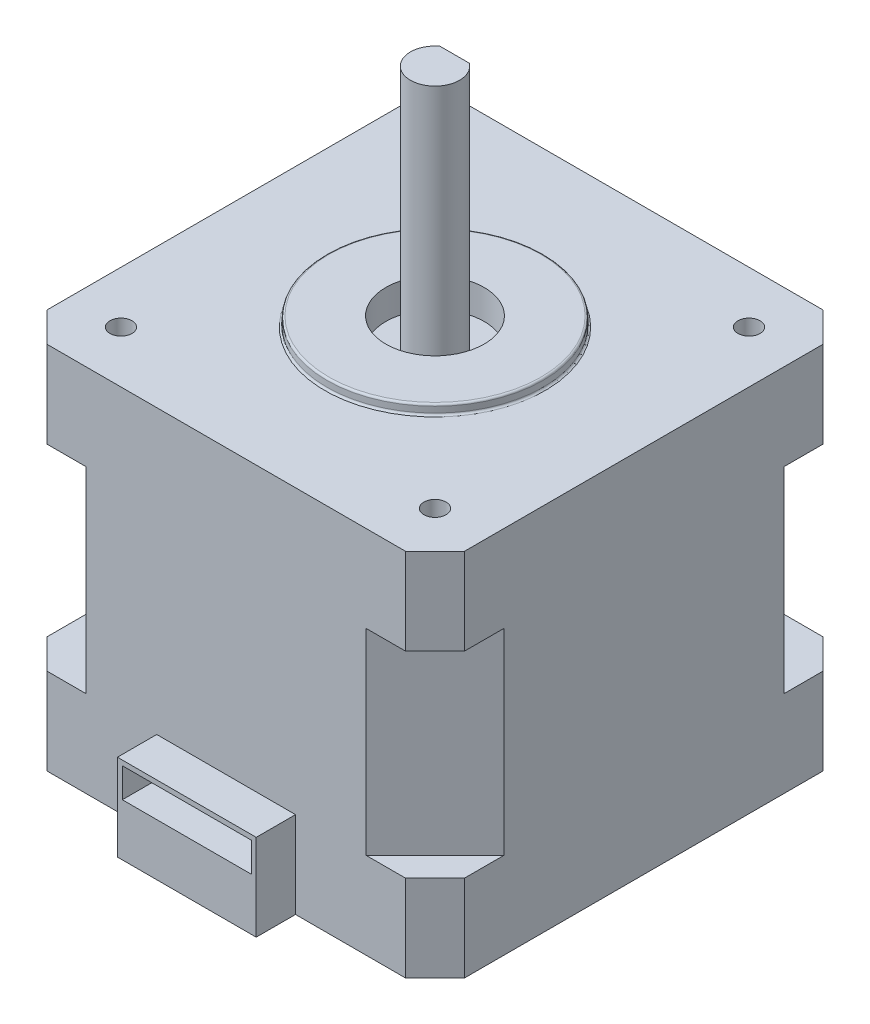
SolidWorks part; units mm, degrees
ref_plane "Front Plane" through (0, 0, 0) normal (0, 0, 1) x (1, 0, 0)
ref_plane "Top Plane" through (0, 0, 0) normal (0, 1, 0) x (1, 0, 0)
ref_plane "Right Plane" through (0, 0, 0) normal (1, 0, 0) x (0, 0, -1)
sketch "Sketch1" plane through (0, 0, 0) normal (0, 1, 0) x (1, 0, 0)
  line L0 (-21.25, 18.25) -> (-18.25, 21.25)
  line L1 (-18.25, -21.25) -> (18.25, -21.25)
  line L2 (-21.25, -18.25) -> (-21.25, 18.25)
  line L3 (-18.25, 21.25) -> (18.25, 21.25)
  line L4 (21.25, -18.25) -> (21.25, 18.25)
  line L5 (-21.25, -21.25) -> (21.25, 21.25) construction
  line L6 (-21.25, 21.25) -> (21.25, -21.25) construction
  line L7 (18.25, 21.25) -> (21.25, 18.25)
  line L8 (18.25, -21.25) -> (21.25, -18.25)
  line L9 (-21.25, -18.25) -> (-18.25, -21.25)
  point P0 (0, 0)
  dimension "D1" = 42.5
  dimension "D2" = 42.5
extrude "Boss-Extrude1" add sketch "Sketch1" along normal mid plane 37.6
sketch "Sketch2" plane through (0, 0, 0) normal (0, 1, 0) x (1, 0, 0)
  line L1 (-21.25, 18.25) -> (-21.25, -18.25) construction
  line L2 (18.25, 21.25) -> (-18.25, 21.25) construction
  line L5 (21.25, -18.25) -> (21.25, 18.25) construction
  line L16 (-21.25, 14.25) -> (-21.25, -14.25)
  line L17 (-21.25, -14.25) -> (-14.25, -21.25)
  line L18 (-14.25, -21.25) -> (14.25, -21.25)
  line L19 (14.25, -21.25) -> (21.25, -14.25)
  line L20 (21.25, -14.25) -> (21.25, 14.25)
  line L21 (21.25, 14.25) -> (14.25, 21.25)
  line L22 (14.25, 21.25) -> (-14.25, 21.25)
  line L23 (-14.25, 21.25) -> (-21.25, 14.25)
  dimension "D1" = 42.5
  dimension "D2" = 42.5
  dimension "D3" = 9.8995
  dimension "D4" = 7
extrude "Cut-Extrude1" cut sketch "Sketch2" against normal mid plane 20 flip side to cut
sketch "Sketch3" plane through (0, 0, 21.25) normal (0, 0, 1) x (1, 0, 0)
  line L0 (-18.25, -18.8) -> (18.25, -18.8) construction
  line L1 (-7.0602, -18.8) -> (7.0602, -18.8)
  line L2 (-7.0602, -18.8) -> (-7.0602, -10)
  line L3 (-7.0602, -10) -> (7.0602, -10)
  line L4 (7.0602, -18.8) -> (7.0602, -10)
  line L5 (-7.0602, -18.8) -> (7.0602, -10) construction
  line L6 (-7.0602, -10) -> (7.0602, -18.8) construction
  line L7 (14.25, -10) -> (18.25, -10) construction
  point P0 (0, -14.4)
extrude "Boss-Extrude2" add sketch "Sketch3" along normal blind 4
sketch "Sketch4" plane through (0, 0, 25.25) normal (0, 0, 1) x (1, 0, 0)
  line L0 (7.0602, -10) -> (-7.0602, -10) construction
  line L1 (-6.5602, -13.5) -> (6.5602, -13.5)
  line L2 (-6.5602, -13.5) -> (-6.5602, -10.5)
  line L3 (-6.5602, -10.5) -> (6.5602, -10.5)
  line L4 (6.5602, -13.5) -> (6.5602, -10.5)
  line L5 (-6.5602, -13.5) -> (6.5602, -10.5) construction
  line L6 (-6.5602, -10.5) -> (6.5602, -13.5) construction
  line L7 (7.0602, -18.8) -> (7.0602, -10) construction
  line L8 (-7.0602, -10) -> (-7.0602, -18.8) construction
  point P0 (0, -12)
  dimension "D4" = 3
  dimension "D1" = 0.5
  dimension "D2" = 0.5
  dimension "D3" = 0.5
extrude "Cut-Extrude2" cut sketch "Sketch4" against normal blind 4
sketch "Sketch5" plane through (0, -18.8, 0) normal (0, -1, 0) x (1, 0, 0)
  circle A0 centre (0, 0) radius 4.5
  dimension "D1" = 9
extrude "Cut-Extrude3" cut sketch "Sketch5" against normal blind 3
sketch "Sketch6" plane through (0, 18.8, 0) normal (0, 1, 0) x (1, 0, 0)
  circle A0 centre (0, 0) radius 11
  dimension "D1" = 22
extrude "Boss-Extrude3" add sketch "Sketch6" along normal blind 1
fillet "Fillet1" radius 0.2 2 edges at (0, 19.8, 11) (0, 18.8, 11)
sketch "Sketch7" plane through (0, 19.8, 0) normal (0, 1, 0) x (1, 0, 0)
  circle A0 centre (0, 0) radius 5
  dimension "D1" = 10
extrude "Cut-Extrude4" cut sketch "Sketch7" against normal blind 3
sketch "Sketch8" plane through (0, 16.8, 0) normal (0, 1, 0) x (1, 0, 0)
  line L0 (-1.5, 2) -> (1.5, 2)
  arc A0 (-1.5, 2) -> (1.5, 2) centre (0, 0) ccw
  dimension "D1" = 5
  dimension "D2" = 4.5
extrude "Boss-Extrude4" add sketch "Sketch8" along normal blind 25 separate body
sketch "Esboço1" plane through (0, 18.8, 0) normal (0, 1, 0) x (1, 0, 0)
  line L4 (-21.25, 18.25) -> (-21.25, -18.25) construction
  line L5 (18.25, 21.25) -> (-18.25, 21.25) construction
  line L6 (-15.975, 15.975) -> (15.975, 15.975) construction
  line L7 (-15.975, 15.975) -> (-15.975, -15.975) construction
  line L8 (-18.25, -21.25) -> (18.25, -21.25) construction
  line L9 (21.25, -18.25) -> (21.25, 18.25) construction
  circle A0 centre (-15.975, 15.975) radius 1.125
  circle A1 centre (15.975, 15.975) radius 1.125
  circle A2 centre (15.975, -15.975) radius 1.125
  circle A3 centre (-15.975, -15.975) radius 1.125
  point P6 (16.5092, 15.975)
  point P7 (15.5528, -12.3756)
  point P8 (16.1198, -16.4052)
  dimension "D1" = 2.25
  dimension "D2" = 5.275
  dimension "D3" = 5.275
  dimension "D6" = 5.275
  dimension "D7" = 5.275
  dimension "D4" = 2
  dimension "D5" = 2
extrude "Corte-extrusão1" cut sketch "Esboço1" against normal blind 5.5
equation "\"D2@Sketch1\"=\"D1@Sketch1\""
equation "\"D2@Sketch2\"=\"D1@Sketch2\""
equation "\"D2@Sketch4\"=\"D1@Sketch4\""
equation "\"D3@Sketch4\"=\"D1@Sketch4\""
equation "\"D6@Esboço1\"=\"D3@Esboço1\""
equation "\"D7@Esboço1\"=\"D2@Esboço1\""
